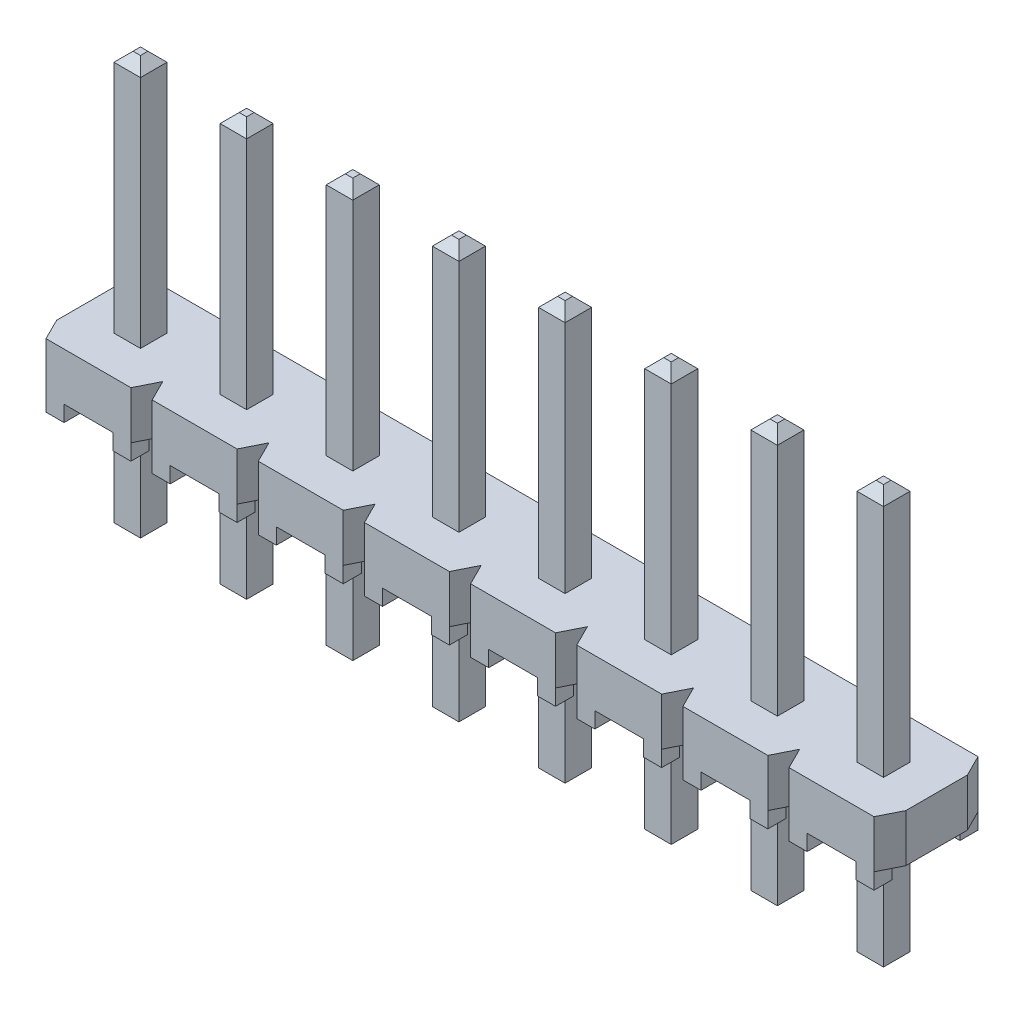
SolidWorks part; units mm, degrees
ref_plane "Front" through (0, 0, 0) normal (0, 0, 1) x (1, 0, 0)
ref_plane "Top" through (0, 0, 0) normal (0, 1, 0) x (1, 0, 0)
ref_plane "Side" through (0, 0, 0) normal (1, 0, 0) x (0, 0, -1)
sketch "Sketch1" plane through (0, 0, 0) normal (0, 1, 0) x (1, 0, 0)
  line L0 (10.16, -1.2446) -> (-10.16, 1.2446) construction
  line L1 (-10.16, 1.2446) -> (10.16, 1.2446)
  line L2 (-10.16, 1.2446) -> (-10.16, -1.2446)
  line L3 (-10.16, -1.2446) -> (10.16, -1.2446)
  line L4 (10.16, 1.2446) -> (10.16, -1.2446)
  dimension "D1" = 20.32
  dimension "D2" = 2.4892
extrude "Base-Extrude" add sketch "Sketch1" along normal mid plane 1.143
sketch "Sketch3" plane through (0, 0.5715, 0) normal (0, 1, 0) x (-1, 0, 0)
  line L0 (7.5339, 0) -> (10.4044, 0) construction
  line L1 (7.366, 1.2446) -> (7.874, 1.2446)
  line L2 (7.366, -1.2446) -> (7.874, -1.2446)
  line L3 (7.874, 1.2446) -> (7.62, 0.7366)
  line L4 (7.874, -1.2446) -> (7.62, -0.7366)
  line L5 (7.62, 0.7366) -> (7.366, 1.2446)
  line L6 (7.62, -0.7366) -> (7.366, -1.2446)
  line L7 (7.62, 1.2446) -> (7.62, 0.7366) construction
  line L8 (7.62, -1.2446) -> (7.62, -0.7366) construction
  line L9 (10.16, 1.2446) -> (-10.16, 1.2446) construction
  line L11 (8.89, -1.4521) -> (8.89, 2.3817) construction
  line L12 (10.16, -0.7366) -> (10.414, -1.2446)
  line L13 (10.16, 0.7366) -> (10.414, 1.2446)
  line L14 (9.906, -1.2446) -> (10.16, -0.7366)
  line L15 (9.906, 1.2446) -> (10.16, 0.7366)
  line L16 (10.414, -1.2446) -> (9.906, -1.2446)
  line L17 (10.414, 1.2446) -> (9.906, 1.2446)
  line L18 (10.16, -1.2446) -> (10.16, 1.2446) construction
  dimension "D1" = 0.508
  dimension "D2" = 0.508
  dimension "D3" = 1.27
  dimension "D4" = 1.27
extrude "Snap Grooves" cut sketch "Sketch3" against normal through all
sketch "Sketch4" plane through (0, -0.5715, 0) normal (0, -1, 0) x (1, 0, 0)
  line L0 (-8.89, 1.3819) -> (-8.89, -1.499) construction
  line L1 (-9.906, 1.2446) -> (-7.874, 1.2446) construction
  line L2 (-9.906, 1.2446) -> (-9.4742, 1.2446)
  line L3 (-9.906, 1.2446) -> (-9.906, 0.8128)
  line L4 (-9.906, 0.8128) -> (-9.4742, 0.8128)
  line L5 (-9.4742, 1.2446) -> (-9.4742, 0.8128)
  line L6 (-8.3058, 1.2446) -> (-8.3058, 0.8128)
  line L7 (-7.874, 0.8128) -> (-8.3058, 0.8128)
  line L8 (-7.874, 1.2446) -> (-7.874, 0.8128)
  line L9 (-7.874, 1.2446) -> (-8.3058, 1.2446)
  line L11 (-10.16, -0.7366) -> (-10.16, 0.7366) construction
  line L12 (-9.3213, 0) -> (-10.8923, 0) construction
  line L14 (-7.874, -1.2446) -> (-8.3058, -1.2446)
  line L15 (-7.874, -1.2446) -> (-7.874, -0.8128)
  line L16 (-7.874, -0.8128) -> (-8.3058, -0.8128)
  line L17 (-8.3058, -1.2446) -> (-8.3058, -0.8128)
  line L18 (-9.4742, -1.2446) -> (-9.4742, -0.8128)
  line L19 (-9.906, -0.8128) -> (-9.4742, -0.8128)
  line L20 (-9.906, -1.2446) -> (-9.906, -0.8128)
  line L21 (-9.906, -1.2446) -> (-9.4742, -1.2446)
  dimension "D1" = 0.4318
  dimension "D2" = 0.4318
  dimension "D3" = 1.27
extrude "Standoffs" add sketch "Sketch4" along normal blind 0.381
pattern_linear "Position Pattern" count 8 spacing 2.54 along (1, 0, 0) of "Snap Grooves", "Standoffs"
ref_plane "Position 1 Plane" through (-8.89, 0, 0) normal (-1, 0, 0) x (0, 0, 1)
sketch "Sketch5" plane through (-8.89, 0, 0) normal (-1, 0, 0) x (0, 0, 1)
  line L0 (0, 6.4135) -> (0, -3.5865) construction
  line L1 (-0.3175, 6.4135) -> (0.3175, 6.4135)
  line L2 (-0.3175, 6.4135) -> (-0.3175, -3.5865)
  line L3 (-0.3175, -3.5865) -> (0.3175, -3.5865)
  line L4 (0.3175, 6.4135) -> (0.3175, -3.5865)
  line L5 (1.2446, -0.5715) -> (1.2446, 0.5715) construction
  line L6 (-0.7366, 0.5715) -> (0.7366, 0.5715) construction
  dimension "D1" = 1.2446
  dimension "D2" = 0.635
  dimension "D3" = 5.842
  dimension "D4" = 10
extrude "Terminal -TH" add sketch "Sketch5" along normal mid plane 0.635
chamfer "T1 Tip1" distance 0.2286 angle 45 8 edges at (-8.5725, 6.4135, 0) (-8.89, 6.4135, -0.3175) (-9.2075, 6.4135, 0) (-8.89, 6.4135, 0.3175) (-8.89, -3.5865, -0.3175) (-9.2075, -3.5865, 0) (-8.89, -3.5865, 0.3175) (-8.5725, -3.5865, 0)
pattern_linear "Terminal Pattern" count 1 spacing 2.54 along (0, 0, 1) count 8 spacing 2.54 along (1, 0, 0) of "Terminal -TH", "T1 Tip1"
ref_plane "Initial -S Polarize Plane" through (11.43, 0, 0) normal (1, 0, 0) x (0, 0, -1)
ref_plane "-S Polarize Plane" through (8.89, 0, 0) normal (1, 0, 0) x (0, 0, -1)
ref_plane "Initial -D Polarize Plane" through (-11.43, 0, 0) normal (-1, 0, 0) x (0, 0, 1)
ref_plane "-D Polarize Plane" through (-10.16, 0, 0) normal (-1, 0, 0) x (0, 0, 1)
